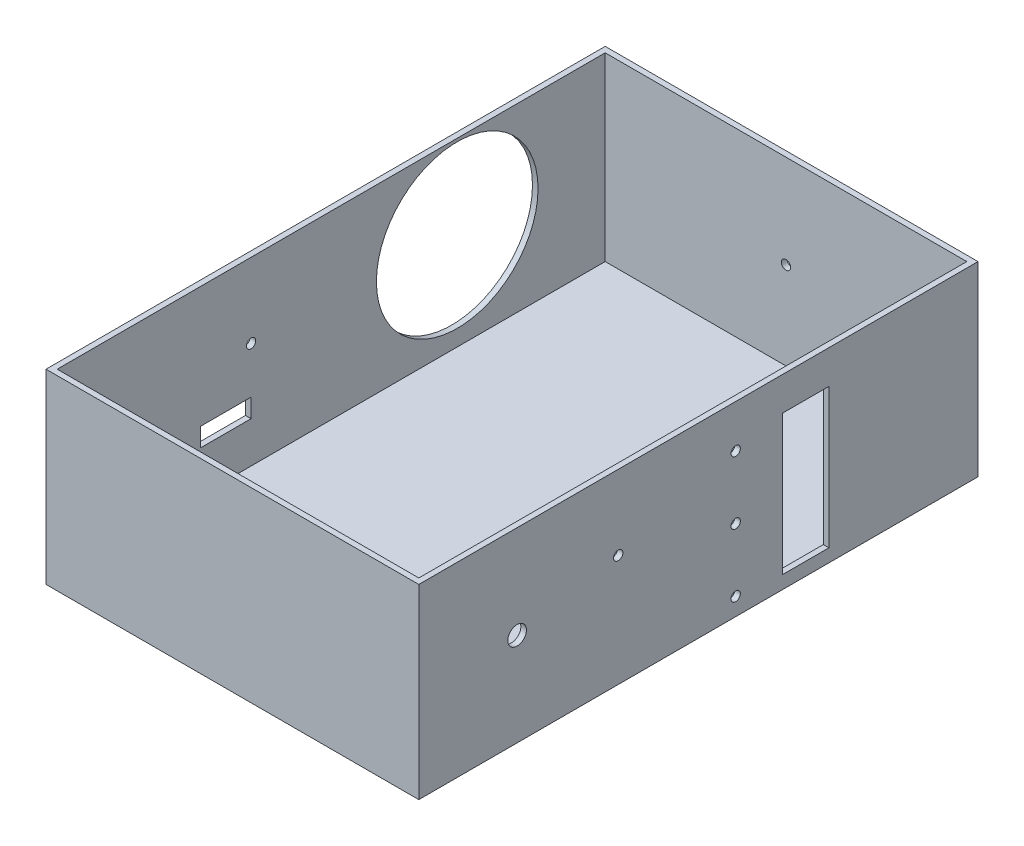
SolidWorks part; units mm, degrees
ref_plane "Plano frontal" through (0, 0, 0) normal (0, 0, 1) x (1, 0, 0)
ref_plane "Plano superior" through (0, 0, 0) normal (0, 1, 0) x (1, 0, 0)
ref_plane "Plano direito" through (0, 0, 0) normal (1, 0, 0) x (0, 0, -1)
sketch "Esboço1" plane through (0, 0, 0) normal (0, 0, 1) x (1, 0, 0)
  line L0 (0, 50) -> (0, -50) construction
  line L5 (-100, 50) -> (100, 50)
  line L6 (-100, 50) -> (-100, -50)
  line L7 (-100, -50) -> (100, -50)
  line L8 (100, 50) -> (100, -50)
  line L9 (-100, 0) -> (100, 0) construction
  point P9 (0, 0)
  dimension "D1" = 200
  dimension "D2" = 100
extrude "Ressalto-extrusão1" add sketch "Esboço1" along normal mid plane 300
sketch "Esboço2" plane through (0, 50, 0) normal (0, 1, 0) x (1, 0, 0)
  line L0 (100, -150) -> (100, 150) construction
  line L1 (-97, 147) -> (97, 147)
  line L2 (-97, 147) -> (-97, -147)
  line L3 (-97, -147) -> (97, -147)
  line L4 (97, 147) -> (97, -147)
  line L5 (-100, -150) -> (-100, 150) construction
  line L6 (100, 150) -> (-100, 150) construction
  line L7 (100, -150) -> (-100, -150) construction
  dimension "D1" = 3
  dimension "D2" = 3
  dimension "D3" = 3
  dimension "D4" = 3
extrude "Corte-extrusão1" cut sketch "Esboço2" against normal blind 97
sketch "Esboço5" plane through (100, 0, 0) normal (1, 0, 0) x (0, 0, -1)
  circle A0 centre (-97.2561, 0) radius 5
  dimension "D1" = 10
extrude "Corte-extrusão4" cut sketch "Esboço5" against normal blind 10
sketch "Esboço7" plane through (0, 0, -150) normal (0, 0, -1) x (-1, 0, 0)
  line L0 (-100, 0) -> (100, 0) construction
  line L1 (0, 50) -> (0, -50) construction
  circle A0 centre (0, 0) radius 2.5
  dimension "D1" = 5
extrude "Corte-extrusão6" cut sketch "Esboço7" against normal blind 10
sketch "Esboço8" plane through (-100, 0, 0) normal (-1, 0, 0) x (0, 0, 1)
  line L0 (56.5, -50) -> (56.5, -20) construction
  line L1 (150, -50) -> (-150, -50) construction
  line L2 (150, 50) -> (-150, 50) construction
  line L3 (43, -15) -> (70, -15)
  line L4 (43, -15) -> (43, -25)
  line L5 (43, -25) -> (70, -25)
  line L6 (70, -15) -> (70, -25)
  line L7 (43, -15) -> (70, -25) construction
  line L8 (43, -25) -> (70, -15) construction
  line L9 (150, 50) -> (150, -50) construction
  dimension "D1" = 27
  dimension "D2" = 10
  dimension "D3" = 65
  dimension "D4" = 80
extrude "Corte-extrusão9" cut sketch "Esboço8" against normal blind 10
sketch "Esboço11" plane through (-100, 0, 0) normal (-1, 0, 0) x (0, 0, 1)
  line L0 (43, -15) -> (43, 10) construction
  line L1 (150, 50) -> (-150, 50) construction
  circle A0 centre (43, 10) radius 2.5
  dimension "D2" = 5
  dimension "D1" = 40
extrude "Corte-extrusão12" cut sketch "Esboço11" against normal through all
sketch "Esboço12" plane through (100, 0, 0) normal (1, 0, 0) x (0, 0, -1)
  line L0 (150, -50) -> (150, 50) construction
  line L1 (45, 32) -> (70, 32)
  line L2 (45, 32) -> (45, -43)
  line L3 (45, -43) -> (70, -43)
  line L4 (70, 32) -> (70, -43)
  line L5 (45, 32) -> (70, -43) construction
  line L6 (45, -43) -> (70, 32) construction
  line L7 (-150, 50) -> (150, 50) construction
  line L8 (70, 27) -> (20, 27) construction
  line L9 (20, -40.5) -> (70, -40.5) construction
  line L10 (20, 27) -> (20, -40.5) construction
  circle A0 centre (20, 27) radius 2.5
  circle A1 centre (20, -6.75) radius 2.5
  circle A2 centre (20, -40.5) radius 2.5
  point P0 (57.5, -5.5)
  point P15 (20, -6.75)
  dimension "D7" = 5
  dimension "D8" = 5
  dimension "D9" = 5
  dimension "D1" = 25
  dimension "D2" = 75
  dimension "D3" = 80
  dimension "D4" = 18
  dimension "D5" = 5
  dimension "D6" = 5
  dimension "D10" = 25
extrude "Corte-extrusão13" cut sketch "Esboço12" against normal blind 10
sketch "Esboço13" plane through (-100, 0, 0) normal (-1, 0, 0) x (0, 0, 1)
  circle A0 centre (-67.6201, 5) radius 43.3583
extrude "Corte-extrusão14" cut sketch "Esboço13" against normal blind 10
